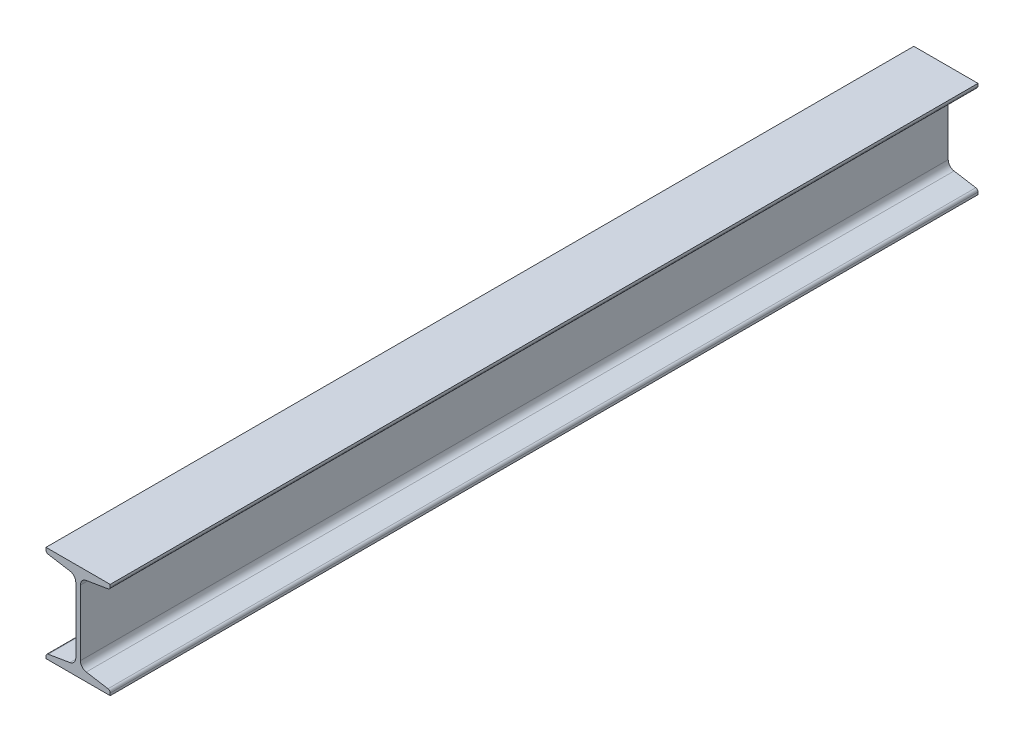
SolidWorks part; units mm, degrees
material "Plain Carbon Steel"
ref_plane "Plane1" through (0, 0, 0) normal (0, 0, 1) x (1, 0, 0)
ref_plane "Plane2" through (0, 0, 0) normal (0, 1, 0) x (-1, 0, 0)
ref_plane "Plane3" through (0, 0, 0) normal (1, 0, 0) x (0, 0, -1)
sketch "Sketch1" plane through (0, 0, 0) normal (0, 0, 1) x (1, 0, 0)
  line L0 (0, 0) -> (0, 4.8279)
  line L1 (0, 4.8279) -> (25.214, 9.0306)
  line L2 (31.369, 16.2963) -> (31.369, 85.3037)
  line L3 (25.214, 92.5694) -> (0, 96.7721)
  line L4 (0, 96.7721) -> (0, 101.6)
  line L5 (0, 101.6) -> (67.6402, 101.6)
  line L6 (67.6402, 101.6) -> (67.6402, 96.7721)
  line L7 (67.6402, 96.7721) -> (42.4262, 92.5694)
  line L8 (36.2712, 85.3037) -> (36.2712, 16.2963)
  line L9 (42.4262, 9.0306) -> (67.6402, 4.8279)
  line L10 (67.6402, 4.8279) -> (67.6402, 0)
  line L11 (67.6402, 0) -> (0, 0)
  line L12 (15.6984, 0) -> (-15.6984, 0) construction
  line L13 (0, -13.7361) -> (0, 13.7361) construction
  line L14 (50.8, 7.4422) -> (31.75, 7.4422) construction
  arc A0 (25.214, 9.0306) -> (31.369, 16.2963) centre (24.003, 16.2963) ccw
  arc A1 (31.369, 85.3037) -> (25.214, 92.5694) centre (24.003, 85.3037) ccw
  arc A2 (42.4262, 92.5694) -> (36.2712, 85.3037) centre (43.6372, 85.3037) ccw
  arc A3 (36.2712, 16.2963) -> (42.4262, 9.0306) centre (43.6372, 16.2963) ccw
  dimension "D7" = 9.463
  dimension "RI" = 7.366
  dimension "BF" = 67.6402
  dimension "D6" = 9.463
  dimension "DEPTH" = 101.6
  dimension "TW" = 4.9022
  dimension "D1" = 69.0073
  dimension "TF" = 7.4422
extrude "BaseSbeam" add sketch "Sketch1" along normal mid plane 914.4
fillet "ToeFillet" radius 2.794 4 edges at (67.6402, 4.8279, 0) (0, 4.8279, 0) (67.6402, 96.7721, 0) (0, 96.7721, 0)
equation "\"d1@Sketch1\" = \"Depth@Sketch1\" - 2*\"TF@Sketch1\" -  2*( \"RI@Sketch1\" * cos(\"D6@Sketch1\"/180*3.141592654))-2*((((\"BF@Sketch1\"-\"TW@Sketch1\")/4)-(\"RI@Sketch1\"-\"RI@Sketch1\"*sin(\"D6@Sketch1\"/180*3.141592654)))*tan(\"D6@Sketch1\"/180*3.141592654))"
